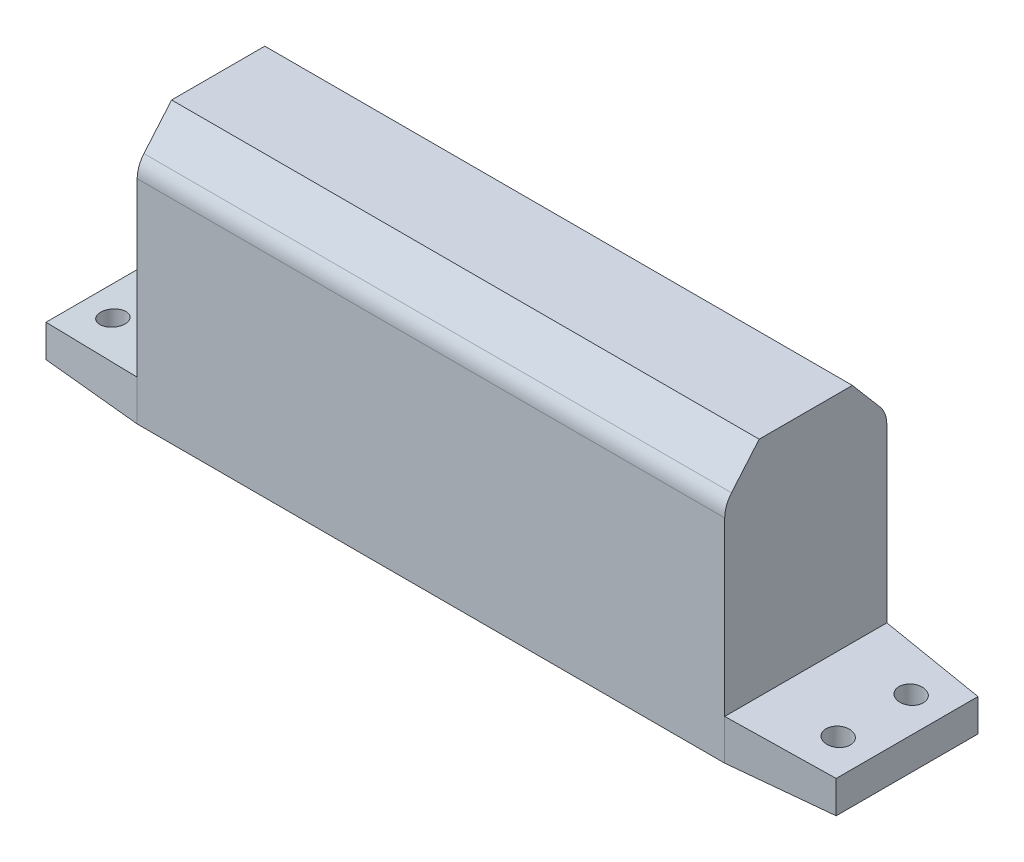
SolidWorks part; units mm, degrees
ref_plane "Front Plane" through (0, 0, 0) normal (0, 0, 1) x (1, 0, 0)
ref_plane "Top Plane" through (0, 0, 0) normal (0, 1, 0) x (1, 0, 0)
ref_plane "Right Plane" through (0, 0, 0) normal (1, 0, 0) x (0, 0, -1)
sketch "Sketch1" plane through (0, 0, 0) normal (0, 1, 0) x (1, 0, 0)
  line L1 (-97.5, 20) -> (97.5, 20)
  line L2 (-97.5, 20) -> (-97.5, -20)
  line L3 (-97.5, -20) -> (97.5, -20)
  line L4 (97.5, 20) -> (97.5, -20)
  line L5 (-97.5, 20) -> (97.5, -20) construction
  line L6 (-97.5, -20) -> (97.5, 20) construction
  point P0 (0, 0)
  dimension "D1" = 195
  dimension "D2" = 40
extrude "Boss-Extrude1" add sketch "Sketch1" along normal blind 10
sketch "Sketch2" plane through (0, 10, 0) normal (0, 1, 0) x (1, 0, 0)
  line L0 (97.5, 20) -> (-97.5, 20) construction
  line L1 (-72.5, 20) -> (72.5, 20)
  line L2 (-72.5, 20) -> (-72.5, -20)
  line L3 (-72.5, -20) -> (72.5, -20)
  line L4 (72.5, 20) -> (72.5, -20)
  line L5 (-72.5, 20) -> (72.5, -20) construction
  line L6 (-72.5, -20) -> (72.5, 20) construction
  point P0 (0, 0)
  dimension "D1" = 145
extrude "Boss-Extrude2" add sketch "Sketch2" along normal blind 55
sketch "Sketch3" plane through (-72.5, 0, 0) normal (-1, 0, 0) x (0, 0, 1)
  line L0 (-11.5, 65) -> (-20, 55)
  line L1 (-20, 65) -> (20, 65) construction
  line L2 (-20, 65) -> (-20, 10) construction
  line L3 (0, 65) -> (0, 45.7151) construction
  line L4 (-20, 55) -> (-20, 68.6426)
  line L5 (-20, 68.6426) -> (-11.5, 65)
  line L6 (11.5, 65) -> (20, 55)
  line L7 (20, 68.6426) -> (11.5, 65)
  line L8 (20, 55) -> (20, 68.6426)
  dimension "D1" = 23
  dimension "D2" = 10
extrude "Cut-Extrude1" cut sketch "Sketch3" against normal blind 237
fillet "Fillet1" radius 7 2 edges at (0, 55, -20) (0, 55, 20)
sketch "Sketch4" plane through (0, 0, -20) normal (0, 0, -1) x (-1, 0, 0)
  line L0 (72.5, 10) -> (97.5, 8)
  line L1 (97.5, 10) -> (97.5, 0) construction
  line L2 (0, 0) -> (0, 20.2541) construction
  line L3 (97.5, 8) -> (97.5, 10)
  line L4 (97.5, 10) -> (72.5, 10)
  line L5 (-97.5, 10) -> (-72.5, 10)
  line L6 (-97.5, 8) -> (-97.5, 10)
  line L7 (-72.5, 10) -> (-97.5, 8)
  dimension "D1" = 8
extrude "Cut-Extrude2" cut sketch "Sketch4" against normal blind 237
sketch "Sketch5" plane through (0, 0, 0) normal (0, -1, 0) x (1, 0, 0)
  line L0 (72.5, 20) -> (97.5, 17.5)
  line L1 (97.5, 17.5) -> (97.5, -17.5)
  line L2 (97.5, 20) -> (72.5, 20)
  line L3 (97.5, 0) -> (88.8176, 0) construction
  line L4 (97.5, 20) -> (97.5, -20) construction
  line L5 (97.5, -20) -> (72.5, -20)
  line L6 (0, 0) -> (0, -31.7114) construction
  line L7 (72.5, -20) -> (97.5, -17.5)
  line L8 (97.5, 20) -> (97.5, -20)
  line L9 (-97.5, -20) -> (-72.5, -20)
  line L10 (-72.5, -20) -> (-97.5, -17.5)
  line L11 (-97.5, 20) -> (-97.5, -20)
  line L12 (-97.5, 17.5) -> (-97.5, -17.5)
  line L13 (-97.5, 20) -> (-72.5, 20)
  line L14 (-72.5, 20) -> (-97.5, 17.5)
  point P4 (97.5, 0)
  line M10 (97.5, -20) -> (97.5, 20)
  line M11 (97.5, 20) -> (-97.5, 20)
  line M12 (-97.5, 20) -> (-97.5, -20)
  line M13 (-97.5, -20) -> (97.5, -20)
  dimension "D1" = 35
extrude "Cut-Extrude3" cut sketch "Sketch5" against normal blind 237 contours L7 M13 M10 | L0 M11 M10 | L14 M11 M12 | L10 M13 M12
sketch "Sketch6" plane through (0, 0, 0) normal (0, -1, 0) x (1, 0, 0)
  line L0 (97.5, 0) -> (87.2038, 0) construction
  line L1 (97.5, 17.5) -> (97.5, -17.5) construction
  line L2 (0, 0) -> (0, -39.3321) construction
  circle A0 centre (89.5, 9) radius 3
  circle A1 centre (89.5, -9) radius 3
  circle A2 centre (-89.5, 9) radius 3
  circle A3 centre (-89.5, -9) radius 3
  dimension "D1" = 12
  dimension "D2" = 6
  dimension "D3" = 5
extrude "Cut-Extrude4" cut sketch "Sketch6" against normal blind 237
sketch "Sketch7" plane through (0, 0, -20) normal (0, 0, -1) x (-1, 0, 0)
  line L0 (0, 0) -> (0, 45) construction
  line L2 (-72.5, 0) -> (72.5, 0) construction
  circle A0 centre (0, 22.5) radius 17.5
  dimension "D1" = 35
  dimension "D2" = 40
extrude "Boss-Extrude3" add sketch "Sketch7" along normal blind 2
sketch "Sketch8" plane through (0, 0, -22) normal (0, 0, -1) x (-1, 0, 0)
  line L1 (8.0829, 8.5) -> (16.1658, 22.5)
  line L2 (16.1658, 22.5) -> (8.0829, 36.5)
  line L3 (8.0829, 36.5) -> (-8.0829, 36.5)
  line L4 (-8.0829, 36.5) -> (-16.1658, 22.5)
  line L5 (-16.1658, 22.5) -> (-8.0829, 8.5)
  line L6 (-8.0829, 8.5) -> (8.0829, 8.5)
  circle A0 centre (0, 22.5) radius 14 construction
  point P1 (0, 8.5)
  dimension "D1" = 28
extrude "Boss-Extrude4" add sketch "Sketch8" along normal blind 6
sketch "Sketch9" plane through (0, 0, -28) normal (0, 0, -1) x (-1, 0, 0)
  line L6 (0, 22.5) -> (5, 27.5) construction
  circle A0 centre (0, 22.5) radius 4.5
  point P0 (0, 22.5)
  dimension "D1" = 9
extrude "Boss-Extrude5" add sketch "Sketch9" along normal blind 10
sketch "Sketch12" plane through (0, 0, -38) normal (0, 0, -1) x (-1, 0, 0)
  line L1 (2.1005, 16.2812) -> (6.4359, 21.2097)
  line L2 (6.4359, 21.2097) -> (4.3354, 27.4285)
  line L3 (4.3354, 27.4285) -> (-2.1005, 28.7188)
  line L4 (-2.1005, 28.7188) -> (-6.4359, 23.7903)
  line L5 (-6.4359, 23.7903) -> (-4.3354, 17.5715)
  line L6 (-4.3354, 17.5715) -> (2.1005, 16.2812)
  circle A0 centre (0, 22.5) radius 5.6845 construction
extrude "Boss-Extrude7" add sketch "Sketch12" along normal blind 5
